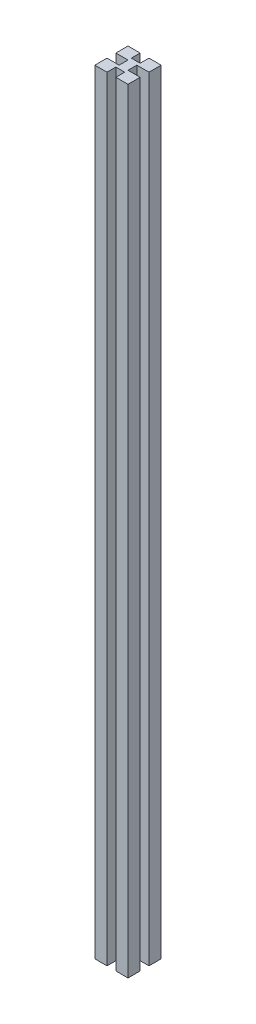
SolidWorks part; units mm, degrees
ref_plane "Front Plane" through (0, 0, 0) normal (0, 0, 1) x (1, 0, 0)
ref_plane "Top Plane" through (0, 0, 0) normal (0, 1, 0) x (1, 0, 0)
ref_plane "Right Plane" through (0, 0, 0) normal (1, 0, 0) x (0, 0, -1)
sketch "Sketch1" plane through (0, 0, 0) normal (0, 1, 0) x (1, 0, 0)
  line L0 (0, 0) -> (8, 0)
  line L1 (8, 0) -> (8, -8)
  line L2 (0, 0) -> (0, -8)
  line L3 (8, -8) -> (8, 0)
  line L4 (8, 22) -> (8, 14)
  line L5 (8, 14) -> (0, 14)
  line L6 (0, 14) -> (0, 22)
  line L7 (8, -8) -> (19, -8)
  line L8 (19, -8) -> (19, 3)
  line L9 (19, 3) -> (8, 3)
  line L10 (8, 14) -> (8, 22)
  line L11 (8, 3) -> (8, 11)
  line L12 (8, 11) -> (19, 11)
  line L13 (19, 11) -> (19, 22)
  line L14 (19, 22) -> (8, 22)
  line L15 (0, 22) -> (-11, 22)
  line L16 (-11, 22) -> (-11, 11)
  line L17 (-11, 11) -> (0, 11)
  line L18 (0, 11) -> (0, 3)
  line L19 (0, 3) -> (-11, 3)
  line L20 (-11, 3) -> (-11, -8)
  line L21 (-11, -8) -> (0, -8)
extrude "Boss-Extrude1" add sketch "Sketch1" along normal blind 700 contours L20 L21 L2 L0 L1 L7 L8 L9 L11 L12 L13 L14 L4 L5 L6 L15 L16 L17 L18 L19
